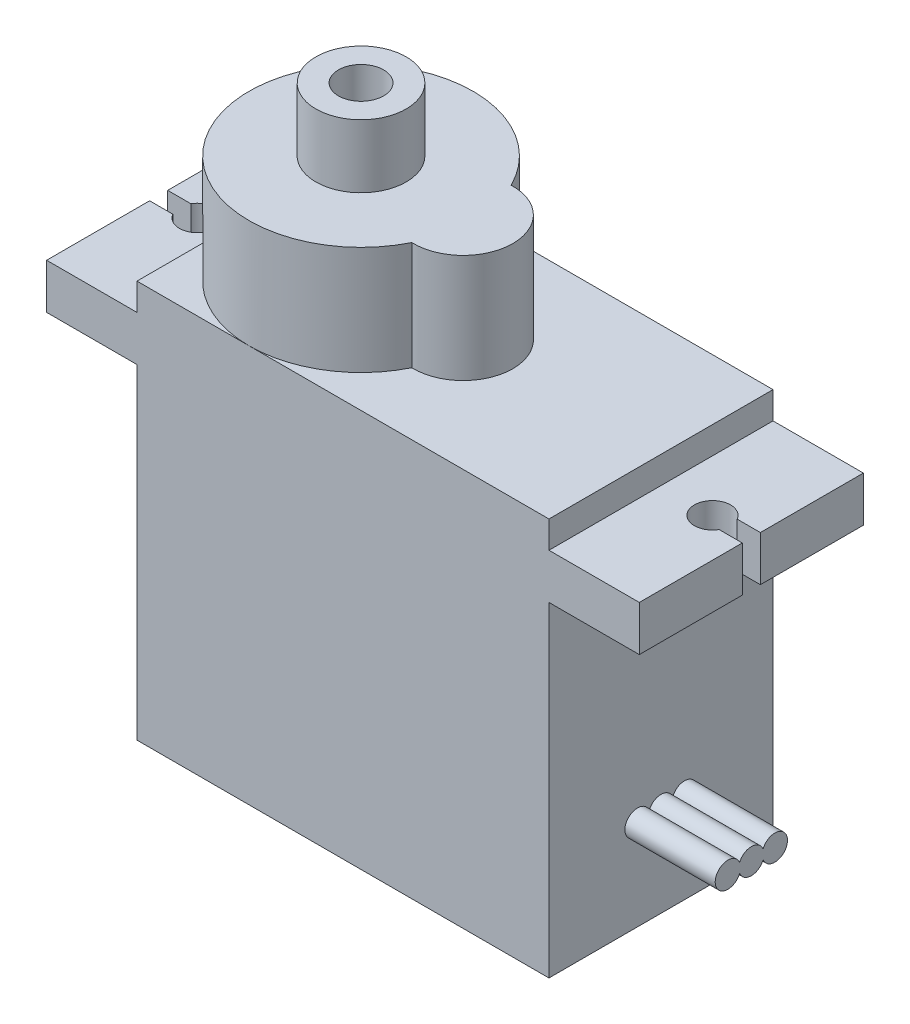
SolidWorks part; units mm, degrees
ref_plane "Front Plane" through (0, 0, 0) normal (0, 0, 1) x (1, 0, 0)
ref_plane "Top Plane" through (0, 0, 0) normal (0, 1, 0) x (1, 0, 0)
ref_plane "Right Plane" through (0, 0, 0) normal (1, 0, 0) x (0, 0, -1)
sketch "Sketch1" plane through (0, 0, 0) normal (0, 1, 0) x (1, 0, 0)
  line L1 (-11.4, 6.2) -> (11.4, 6.2)
  line L2 (-11.4, 6.2) -> (-11.4, -6.2)
  line L3 (-11.4, -6.2) -> (11.4, -6.2)
  line L4 (11.4, 6.2) -> (11.4, -6.2)
  point P4 (0, 6.2)
  point P6 (-11.4, 0)
  dimension "D1" = 22.8
  dimension "D2" = 12.4
extrude "Boss-Extrude1" add sketch "Sketch1" along normal blind 22
sketch "Sketch2" plane through (0, 22, 0) normal (0, 1, 0) x (1, 0, 0)
  line L0 (11.4, 6.2) -> (-11.4, 6.2) construction
  line L1 (-11.4, 6.2) -> (-11.4, -6.2) construction
  line L2 (-11.4, -6.2) -> (11.4, -6.2) construction
  line L6 (0, 0) -> (0.45, 0) construction
  arc A0 (0.3575, 2.7484) -> (0.3575, -2.7484) centre (-5.2, 0) ccw
  arc A1 (0.3575, -2.7484) -> (0.3575, 2.7484) centre (0.45, 0) ccw
  dimension "D2" = 14.6
  dimension "D1" = 2.75
extrude "Boss-Extrude3" add sketch "Sketch2" along normal blind 6
sketch "Sketch3" plane through (0, 28, 0) normal (0, 1, 0) x (1, 0, 0)
  circle A0 centre (-5.2, 0) radius 2.5
  circle A1 centre (-5.2, 0) radius 1.25
  arc A2 (0.3575, 2.7484) -> (0.3575, -2.7484) centre (-5.2, 0) ccw construction
  dimension "D1" = 5
  dimension "D2" = 2.5
extrude "Boss-Extrude4" add sketch "Sketch3" along normal blind 3.5
ref_plane "Plane1" through (0, 18, 0) normal (0, 1, 0) x (1, 0, 0)
sketch "Sketch4" plane through (0, 18, 0) normal (0, 1, 0) x (1, 0, 0)
  line L0 (-16.4, -0.5) -> (-16.4, -6.2)
  line L1 (-16.4, 6.2) -> (-11.4, 6.2)
  line L2 (-16.4, 6.2) -> (-16.4, 0.5)
  line L3 (-16.4, -6.2) -> (-11.4, -6.2)
  line L4 (-11.4, 6.2) -> (-11.4, -6.2)
  line L5 (-16.4, 0.5) -> (-15.116, 0.5)
  line L6 (-14.25, 0) -> (0, 0) construction
  line L7 (-16.4, -0.5) -> (-15.116, -0.5)
  arc A0 (-15.116, -0.5) -> (-15.116, 0.5) centre (-14.25, 0) ccw
  dimension "D2" = 1
  dimension "D1" = 5
  dimension "D3" = 1
  dimension "D4" = 14.25
extrude "Boss-Extrude5" add sketch "Sketch4" along normal blind 2.5
sketch "Sketch5" plane through (0, 18, 0) normal (0, -1, 0) x (1, 0, 0)
  line L24 (-11.4, -5.2) -> (-11.4, 5.2)
  line L30 (-11.4, -5.2) -> (-15.4, -5.2)
  line L31 (-15.4, -5.2) -> (-15.4, -1.6363)
  line L34 (-15.4, 1.6363) -> (-15.4, 5.2)
  line L35 (-15.4, 5.2) -> (-11.4, 5.2)
  line L36 (-11.4, -5.2) -> (-15.4, -5.2)
  line L37 (-15.4, -5.2) -> (-15.4, -1.6363)
  line L40 (-15.4, 1.6363) -> (-15.4, 5.2)
  line L41 (-15.4, 5.2) -> (-11.4, 5.2)
  arc A5 (-15.4, -1.6363) -> (-15.4, 1.6363) centre (-14.25, 0) ccw
  arc A6 (-15.4, -1.6363) -> (-15.4, 1.6363) centre (-14.25, 0) ccw
  dimension "D1" = 1
extrude "Cut-Extrude1" cut sketch "Sketch5" against normal blind 1
mirror "Mirror1" about plane through (0, 0, 0) normal (1, 0, 0) of "Cut-Extrude1", "Boss-Extrude5"
sketch "Sketch6" plane through (11.4, 0, 0) normal (1, 0, 0) x (0, 0, -1)
  line L0 (-1.3, 5) -> (1.3, 5) construction
  line L1 (0, 4.3) -> (0, 0) construction
  line L2 (-6.2, 0) -> (6.2, 0) construction
  arc A0 (-0.65, 4.7402) -> (0.65, 4.7402) centre (0, 5) ccw
  arc A1 (0.65, 4.7402) -> (0.65, 5.2598) centre (1.3, 5) ccw
  arc A2 (-0.65, 5.2598) -> (-0.65, 4.7402) centre (-1.3, 5) ccw
  arc A3 (0.65, 5.2598) -> (-0.65, 5.2598) centre (0, 5) ccw
  dimension "D1" = 1.4
  dimension "D2" = 2
  dimension "D3" = 5
extrude "Boss-Extrude6" add sketch "Sketch6" along normal blind 5
